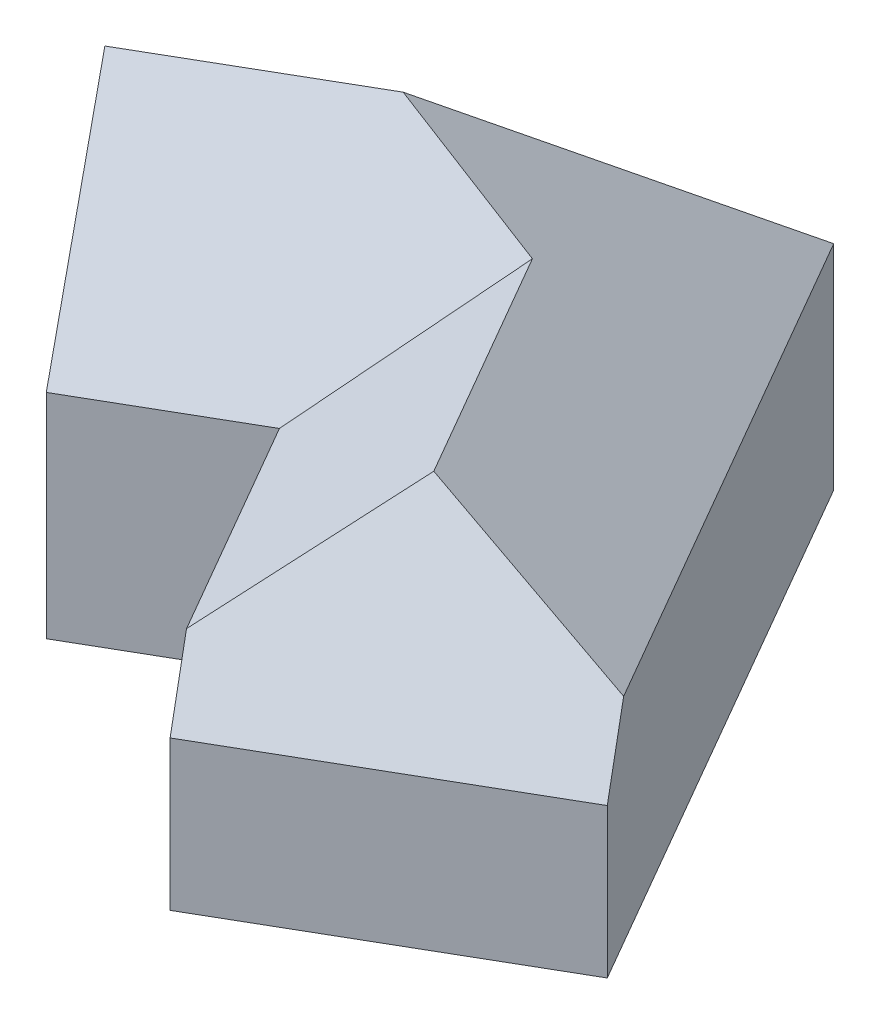
SolidWorks part; units mm, degrees
ref_plane "Front" through (0, 0, 0) normal (0, 0, 1) x (1, 0, 0)
ref_plane "Top" through (0, 0, 0) normal (0, 1, 0) x (1, 0, 0)
ref_plane "Right" through (0, 0, 0) normal (1, 0, 0) x (0, 0, -1)
sketch "Sketch1" plane through (0, 0, 0) normal (0, 1, 0) x (1, 0, 0)
  line L0 (0, 0) -> (72.5, -125.5737)
  line L1 (72.5, -125.5737) -> (7.5481, -163.0737)
  line L2 (7.5481, -163.0737) -> (-27.4519, -102.4519)
  line L3 (-27.4519, -102.4519) -> (-62.0929, -122.4519)
  line L4 (-62.0929, -122.4519) -> (-99.5929, -57.5)
  line L5 (-99.5929, -57.5) -> (0, 0)
  line L6 (0, 0) -> (39.3004, 0) construction
  dimension "D1" = 60
  dimension "D2" = 145
  dimension "D3" = 115
  dimension "D4" = 75
  dimension "D5" = 40
extrude "Extrude1" add sketch "Sketch1" along normal blind 50
sketch "Sketch2" plane through (-99.5929, 0, 57.5) normal (-0.866, 0, 0.5) x (0.5, 0, 0.866)
  line L0 (75, 50) -> (0, 50)
  line L1 (0, 50) -> (37.5, 94.6908)
  line L2 (37.5, 94.6908) -> (75, 50)
  dimension "D1" = 50
extrude "Extrude2" add sketch "Sketch2" against normal blind 115
sketch "Sketch3" plane through (72.5, 0, 125.5737) normal (0.5, 0, 0.866) x (0.866, 0, -0.5)
  line L0 (0, 50) -> (-75, 50)
  line L1 (-75, 50) -> (-37.5, 76.2578)
  line L2 (-37.5, 76.2578) -> (0, 50)
  dimension "D1" = 35
extrude "Extrude3" add sketch "Sketch3" against normal blind 105
sketch "Sketch4" plane through (72.5, 0, 125.5737) normal (0.5, 0, 0.866) x (0.866, 0, -0.5)
  line L0 (0, 50) -> (0, 113.527)
  line L1 (0, 113.527) -> (-90.7259, 113.527)
  line L2 (0, 50) -> (-90.7259, 113.527)
extrude "Cut-Extrude1" cut sketch "Sketch4" against normal blind 155
sketch "Sketch5" plane through (0, 0, 0) normal (0.866, 0, -0.5) x (-0.5, 0, -0.866)
  line L0 (-145, 35) -> (-97.8615, 102.3207)
  line L1 (-145, 50) -> (-145, 0) construction
  line L2 (-97.8615, 102.3207) -> (-145, 102.3207)
  line L3 (-145, 102.3207) -> (-145, 35)
  line L4 (-145, 0) -> (0, 0) construction
  line L5 (-145, 35) -> (-113.4768, 35) construction
  dimension "D1" = 35
  dimension "D2" = 55
extrude "Cut-Extrude2" cut sketch "Sketch5" against normal blind 75
ref_plane "BC Dihedral Angle Plane" through (-18.262, 72.3454, 32.1942) normal (-0.4224, 0.5168, 0.7446) x (0.9064, 0.2408, 0.347)
